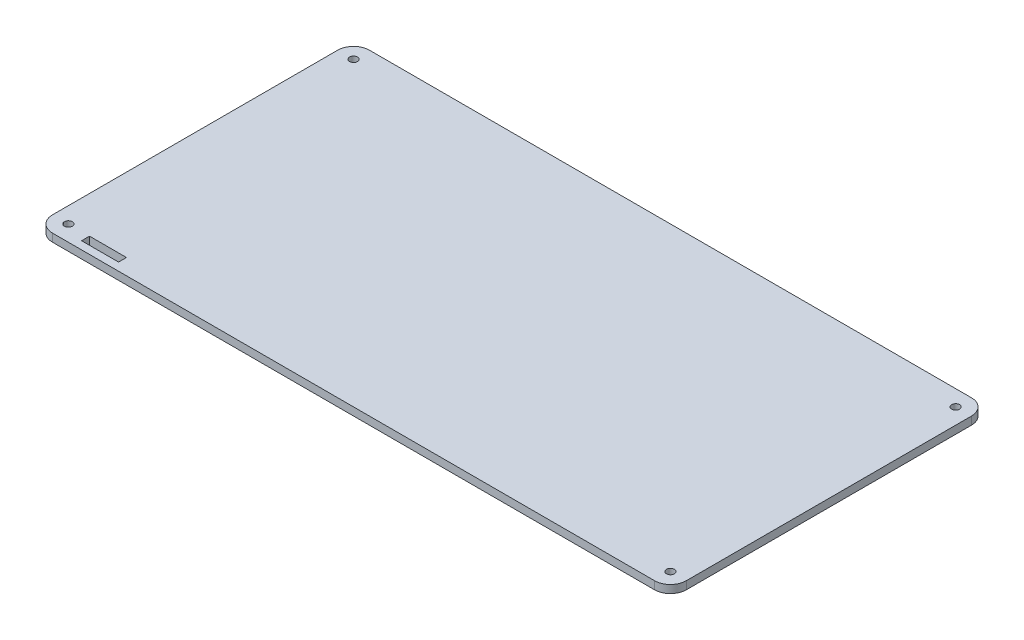
SolidWorks part; units mm, degrees
material "Acrylic (Medium-high impact)"
ref_plane "Front Plane" through (0, 0, 0) normal (0, 0, 1) x (1, 0, 0)
ref_plane "Top Plane" through (0, 0, 0) normal (0, 1, 0) x (1, 0, 0)
ref_plane "Right Plane" through (0, 0, 0) normal (1, 0, 0) x (0, 0, -1)
sketch "Sketch1" plane through (0, 0, 0) normal (0, 1, 0) x (1, 0, 0)
  line L1 (-120, 60) -> (120, 60)
  line L2 (-120, 60) -> (-120, -60)
  line L3 (-120, -60) -> (120, -60)
  line L4 (120, 60) -> (120, -60)
  line L5 (-106, -54) -> (-92, -54)
  line L6 (-106, -54) -> (-106, -57)
  line L7 (-106, -57) -> (-92, -57)
  line L8 (-92, -54) -> (-92, -57)
  point P4 (0, 60)
  point P6 (120, 0)
  dimension "D1" = 240
  dimension "D2" = 120
  dimension "D3" = 3
  dimension "D4" = 14
  dimension "D5" = 3
  dimension "D6" = 14
extrude "Boss-Extrude1" add sketch "Sketch1" along normal blind 3
fillet "Fillet1" radius 6 4 edges at (-120, 1.5, -60) (120, 1.5, -60) (-120, 1.5, 60) (120, 1.5, 60)
sketch "Sketch2" plane through (0, 0, 0) normal (0, 1, 0) x (1, 0, 0)
  circle A0 centre (-114, 54) radius 1.5
  circle A1 centre (114, 54) radius 1.5
  circle A2 centre (-114, -54) radius 1.5
  circle A3 centre (114, -54) radius 1.5
  arc A4 (-114, 60) -> (-120, 54) centre (-114, 54) ccw construction
  arc A5 (-120, -54) -> (-114, -60) centre (-114, -54) ccw construction
  arc A6 (114, -60) -> (120, -54) centre (114, -54) ccw construction
  arc A7 (120, 54) -> (114, 60) centre (114, 54) ccw construction
  dimension "D1" = 3
extrude "Cut-Extrude2" cut sketch "Sketch2" along normal through all
